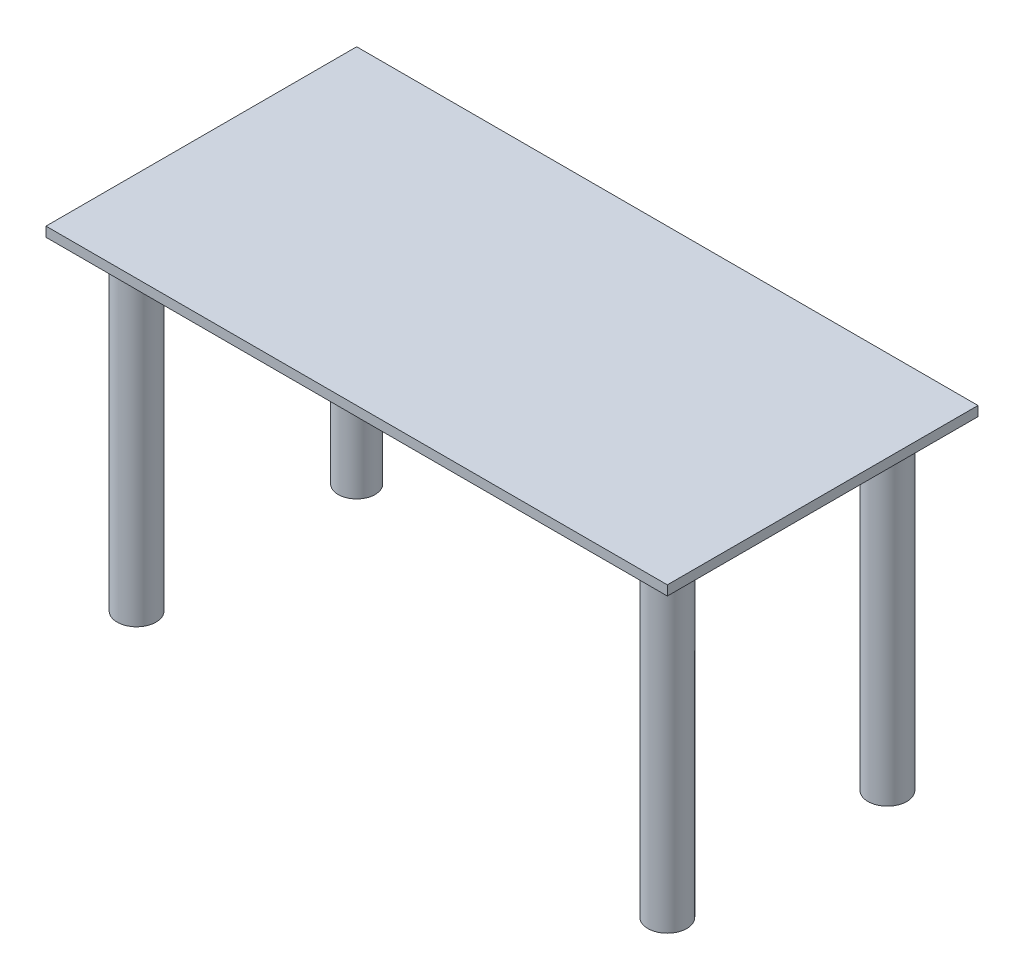
SolidWorks part; units mm, degrees
ref_plane "Front Plane" through (0, 0, 0) normal (0, 0, 1) x (1, 0, 0)
ref_plane "Top Plane" through (0, 0, 0) normal (0, 1, 0) x (1, 0, 0)
ref_plane "Right Plane" through (0, 0, 0) normal (1, 0, 0) x (0, 0, -1)
sketch "Sketch1" plane through (0, 0, 0) normal (0, 1, 0) x (1, 0, 0)
  line L1 (-609.6, 304.8) -> (609.6, 304.8)
  line L2 (-609.6, 304.8) -> (-609.6, -304.8)
  line L3 (-609.6, -304.8) -> (609.6, -304.8)
  line L4 (609.6, 304.8) -> (609.6, -304.8)
  line L5 (-609.6, 304.8) -> (609.6, -304.8) construction
  line L6 (-609.6, -304.8) -> (609.6, 304.8) construction
  point P0 (0, 0)
  dimension "D1" = 609.6
  dimension "D2" = 1219.2
extrude "Boss-Extrude1" add sketch "Sketch1" along normal blind 19.05
sketch "Sketch2" plane through (0, 0, 0) normal (0, -1, 0) x (1, 0, 0)
  line L0 (-609.6, 304.8) -> (609.6, 304.8) construction
  line L1 (-609.6, -304.8) -> (-609.6, 304.8) construction
  line L2 (609.6, -304.8) -> (-609.6, -304.8) construction
  line L3 (609.6, 304.8) -> (609.6, -304.8) construction
  circle A0 centre (-520.7, 215.9) radius 63.5
  circle A1 centre (-520.7, -215.9) radius 63.5
  circle A2 centre (520.7, 215.9) radius 63.5
  circle A3 centre (520.7, -215.9) radius 63.5
  dimension "D1" = 127
  dimension "D2" = 88.9
  dimension "D3" = 88.9
  dimension "D4" = 88.9
  dimension "D5" = 88.9
  dimension "D6" = 127
  dimension "D7" = 127
  dimension "D8" = 88.9
  dimension "D9" = 88.9
  dimension "D10" = 127
  dimension "D11" = 88.9
  dimension "D12" = 88.9
extrude "Boss-Extrude2" add sketch "Sketch2" along normal blind 25.4
sketch "Sketch3" plane through (0, -25.4, 0) normal (0, -1, 0) x (1, 0, 0)
  circle A0 centre (-520.7, 215.9) radius 38.1
  circle A1 centre (-520.7, -215.9) radius 36.1655
  circle A2 centre (520.7, 215.9) radius 38.1
  circle A3 centre (520.7, -215.9) radius 38.1
  circle A4 centre (-520.7, -215.9) radius 63.5 construction
  circle A5 centre (520.7, -215.9) radius 63.5 construction
  circle A6 centre (520.7, 215.9) radius 63.5 construction
  point P9 (0, 0)
  dimension "D1" = 76.2
  dimension "D3" = 0
  dimension "D4" = 0
  dimension "D2" = 0
extrude "Boss-Extrude3" add sketch "Sketch3" along normal blind 609.6
sketch "Sketch4" plane through (0, -635, 0) normal (0, -1, 0) x (1, 0, 0)
  circle A0 centre (-520.7, 215.9) radius 31.75
  circle A1 centre (520.7, 215.9) radius 31.75
  circle A2 centre (520.7, -215.9) radius 31.75
  circle A3 centre (-520.7, -215.9) radius 31.75
  circle A4 centre (-520.7, -215.9) radius 36.1655 construction
  circle A5 centre (520.7, 215.9) radius 38.1 construction
  circle A6 centre (520.7, -215.9) radius 38.1 construction
  dimension "D1" = 63.5
  dimension "D2" = 0
  dimension "D3" = 0
  dimension "D4" = 0
extrude "Cut-Extrude1" cut sketch "Sketch4" against normal blind 584.2
